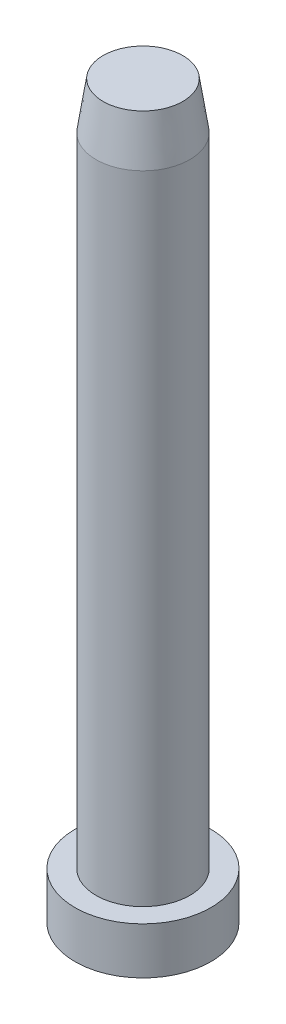
SolidWorks part; units mm, degrees
material "1.0045 (S355JR)"
ref_plane "Front Plane" through (0, 0, 0) normal (0, 0, 1) x (1, 0, 0)
ref_plane "Top Plane" through (0, 0, 0) normal (0, 1, 0) x (1, 0, 0)
ref_plane "Right Plane" through (0, 0, 0) normal (1, 0, 0) x (0, 0, -1)
sketch "Sketch5" plane through (0, 0, 0) normal (0, 0, 1) x (1, 0, 0)
  line L0 (0, 0) -> (7.25, 0)
  line L1 (7.25, 0) -> (7.25, 5)
  line L2 (7.25, 5) -> (5, 5)
  line L3 (5, 5) -> (5, 73)
  line L4 (4.25, 78) -> (5, 73)
  line L5 (4.25, 78) -> (0, 78)
  line L6 (0, 78) -> (0, 0) construction
  line L7 (0, 0) -> (0, 78)
  point P3 (4.25, 78)
  dimension "D1" = 7.25
  dimension "D2" = 5
  dimension "D3" = 2.25
  dimension "D4" = 68
  dimension "D5" = 5
  dimension "D6" = 0.75
  dimension "D7" = 4.25
revolve "Revolve1" add sketch "Sketch5" angle 360 about L6
